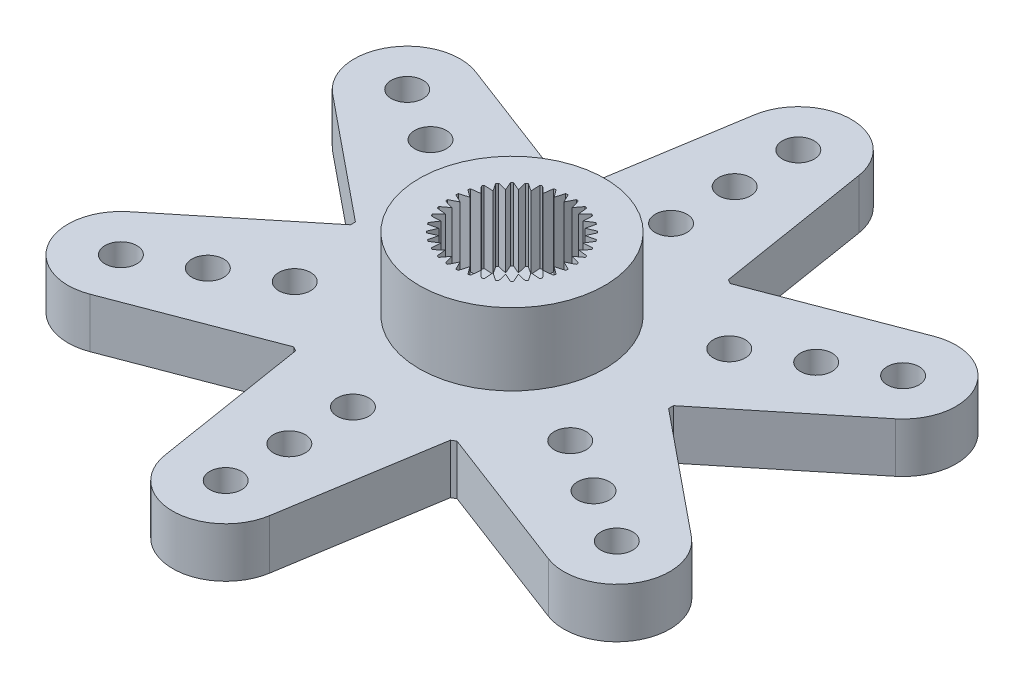
SolidWorks part; units mm, degrees
ref_plane "Front Plane" through (0, 0, 0) normal (0, 0, 1) x (1, 0, 0)
ref_plane "Top Plane" through (0, 0, 0) normal (0, 1, 0) x (1, 0, 0)
ref_plane "Right Plane" through (0, 0, 0) normal (1, 0, 0) x (0, 0, -1)
ref_plane "Plane1" through (0, 2.35, 0) normal (0, 1, 0) x (1, 0, 0)
sketch "Sketch1" plane through (0, 2.35, 0) normal (0, 1, 0) x (1, 0, 0)
  line L0 (-3.65, -6.5519) -> (-2.4683, -13.8971)
  line L1 (2.4683, -13.8971) -> (3.65, -6.5519)
  line L2 (3.8491, -6.4369) -> (10.8011, -9.0861)
  line L3 (13.2694, -4.811) -> (7.4991, -0.115)
  line L4 (7.4991, 0.115) -> (13.2694, 4.811)
  line L5 (10.8011, 9.0861) -> (3.8491, 6.4369)
  line L6 (3.65, 6.5519) -> (2.4683, 13.8971)
  line L7 (-2.4683, 13.8971) -> (-3.65, 6.5519)
  line L8 (-3.8491, 6.4369) -> (-10.8011, 9.0861)
  line L9 (-13.2694, 4.811) -> (-7.4991, 0.115)
  line L10 (-7.4991, -0.115) -> (-13.2694, -4.811)
  line L11 (-10.8011, -9.0861) -> (-3.8491, -6.4369)
  arc A0 (-3.8491, -6.4369) -> (-3.65, -6.5519) centre (0, 0) ccw
  arc A1 (-2.4683, -13.8971) -> (2.4683, -13.8971) centre (0, -13.5) ccw
  arc A2 (3.65, -6.5519) -> (3.8491, -6.4369) centre (0, 0) ccw
  arc A3 (10.8011, -9.0861) -> (13.2694, -4.811) centre (11.6913, -6.75) ccw
  arc A4 (7.4991, -0.115) -> (7.4991, 0.115) centre (0, 0) ccw
  arc A5 (13.2694, 4.811) -> (10.8011, 9.0861) centre (11.6913, 6.75) ccw
  arc A6 (3.8491, 6.4369) -> (3.65, 6.5519) centre (0, 0) ccw
  arc A7 (2.4683, 13.8971) -> (-2.4683, 13.8971) centre (0, 13.5) ccw
  arc A8 (-3.65, 6.5519) -> (-3.8491, 6.4369) centre (0, 0) ccw
  arc A9 (-10.8011, 9.0861) -> (-13.2694, 4.811) centre (-11.6913, 6.75) ccw
  arc A10 (-7.4991, 0.115) -> (-7.4991, -0.115) centre (0, 0) ccw
  arc A11 (-13.2694, -4.811) -> (-10.8011, -9.0861) centre (-11.6913, -6.75) ccw
extrude "Boss-Extrude1" add sketch "Sketch1" against normal blind 2.35
sketch "Sketch2" plane through (0, 2.35, 0) normal (0, 1, 0) x (-1, 0, 0)
  circle A0 centre (0, 0) radius 4.375
extrude "Boss-Extrude2" add sketch "Sketch2" along normal blind 3.4
sketch "Sketch3" plane through (0, 5.75, 0) normal (0, 1, 0) x (-1, 0, 0)
  line L0 (0.6873, 2.7659) -> (0.4254, 2.4128)
  line L1 (0.4254, 2.4128) -> (0.3001, 2.8342)
  line L2 (0.1966, 2.8432) -> (0, 2.45)
  line L3 (0, 2.45) -> (-0.1966, 2.8432)
  line L4 (-0.3001, 2.8342) -> (-0.4254, 2.4128)
  line L5 (-0.4254, 2.4128) -> (-0.6873, 2.7659)
  line L6 (-0.7877, 2.739) -> (-0.8379, 2.3022)
  line L7 (-0.8379, 2.3022) -> (-1.1572, 2.6045)
  line L8 (-1.2513, 2.5606) -> (-1.225, 2.1218)
  line L9 (-1.225, 2.1218) -> (-1.5919, 2.364)
  line L10 (-1.677, 2.3044) -> (-1.5748, 1.8768)
  line L11 (-1.5748, 1.8768) -> (-1.9782, 2.0517)
  line L12 (-2.0517, 1.9782) -> (-1.8768, 1.5748)
  line L13 (-1.8768, 1.5748) -> (-2.3044, 1.677)
  line L14 (-2.364, 1.5919) -> (-2.1218, 1.225)
  line L15 (-2.1218, 1.225) -> (-2.5606, 1.2513)
  line L16 (-2.6045, 1.1572) -> (-2.3022, 0.8379)
  line L17 (-2.3022, 0.8379) -> (-2.739, 0.7877)
  line L18 (-2.7659, 0.6873) -> (-2.4128, 0.4254)
  line L19 (-2.4128, 0.4254) -> (-2.8342, 0.3001)
  line L20 (-2.8432, 0.1966) -> (-2.45, 0)
  line L21 (-2.45, 0) -> (-2.8432, -0.1966)
  line L22 (-2.8342, -0.3001) -> (-2.4128, -0.4254)
  line L23 (-2.4128, -0.4254) -> (-2.7659, -0.6873)
  line L24 (-2.739, -0.7877) -> (-2.3022, -0.8379)
  line L25 (-2.3022, -0.8379) -> (-2.6045, -1.1572)
  line L26 (-2.5606, -1.2513) -> (-2.1218, -1.225)
  line L27 (-2.1218, -1.225) -> (-2.364, -1.5919)
  line L28 (-2.3044, -1.677) -> (-1.8768, -1.5748)
  line L29 (-1.8768, -1.5748) -> (-2.0517, -1.9782)
  line L30 (-1.9782, -2.0517) -> (-1.5748, -1.8768)
  line L31 (-1.5748, -1.8768) -> (-1.677, -2.3044)
  line L32 (-1.5919, -2.364) -> (-1.225, -2.1218)
  line L33 (-1.225, -2.1218) -> (-1.2513, -2.5606)
  line L34 (-1.1572, -2.6045) -> (-0.8379, -2.3022)
  line L35 (-0.8379, -2.3022) -> (-0.7877, -2.739)
  line L36 (-0.6873, -2.7659) -> (-0.4254, -2.4128)
  line L37 (-0.4254, -2.4128) -> (-0.3001, -2.8342)
  line L38 (-0.1966, -2.8432) -> (0, -2.45)
  line L39 (0, -2.45) -> (0.1966, -2.8432)
  line L40 (0.3001, -2.8342) -> (0.4254, -2.4128)
  line L41 (0.4254, -2.4128) -> (0.6873, -2.7659)
  line L42 (0.7877, -2.739) -> (0.8379, -2.3022)
  line L43 (0.8379, -2.3022) -> (1.1572, -2.6045)
  line L44 (1.2513, -2.5606) -> (1.225, -2.1218)
  line L45 (1.225, -2.1218) -> (1.5919, -2.364)
  line L46 (1.677, -2.3044) -> (1.5748, -1.8768)
  line L47 (1.5748, -1.8768) -> (1.9782, -2.0517)
  line L48 (2.0517, -1.9782) -> (1.8768, -1.5748)
  line L49 (1.8768, -1.5748) -> (2.3044, -1.677)
  line L50 (2.364, -1.5919) -> (2.1218, -1.225)
  line L51 (2.1218, -1.225) -> (2.5606, -1.2513)
  line L52 (2.6045, -1.1572) -> (2.3022, -0.8379)
  line L53 (2.3022, -0.8379) -> (2.739, -0.7877)
  line L54 (2.7659, -0.6873) -> (2.4128, -0.4254)
  line L55 (2.4128, -0.4254) -> (2.8342, -0.3001)
  line L56 (2.8432, -0.1966) -> (2.45, 0)
  line L57 (2.45, 0) -> (2.8432, 0.1966)
  line L58 (2.8342, 0.3001) -> (2.4128, 0.4254)
  line L59 (2.4128, 0.4254) -> (2.7659, 0.6873)
  line L60 (2.739, 0.7877) -> (2.3022, 0.8379)
  line L61 (2.3022, 0.8379) -> (2.6045, 1.1572)
  line L62 (2.5606, 1.2513) -> (2.1218, 1.225)
  line L63 (2.1218, 1.225) -> (2.364, 1.5919)
  line L64 (2.3044, 1.677) -> (1.8768, 1.5748)
  line L65 (1.8768, 1.5748) -> (2.0517, 1.9782)
  line L66 (1.9782, 2.0517) -> (1.5748, 1.8768)
  line L67 (1.5748, 1.8768) -> (1.677, 2.3044)
  line L68 (1.5919, 2.364) -> (1.225, 2.1218)
  line L69 (1.225, 2.1218) -> (1.2513, 2.5606)
  line L70 (1.1572, 2.6045) -> (0.8379, 2.3022)
  line L71 (0.8379, 2.3022) -> (0.7877, 2.739)
  arc A0 (0.3001, 2.8342) -> (0.1966, 2.8432) centre (0, 0) ccw
  arc A1 (-0.1966, 2.8432) -> (-0.3001, 2.8342) centre (0, 0) ccw
  arc A2 (-0.6873, 2.7659) -> (-0.7877, 2.739) centre (0, 0) ccw
  arc A3 (-1.1572, 2.6045) -> (-1.2513, 2.5606) centre (0, 0) ccw
  arc A4 (-1.5919, 2.364) -> (-1.677, 2.3044) centre (0, 0) ccw
  arc A5 (-1.9782, 2.0517) -> (-2.0517, 1.9782) centre (0, 0) ccw
  arc A6 (-2.3044, 1.677) -> (-2.364, 1.5919) centre (0, 0) ccw
  arc A7 (-2.5606, 1.2513) -> (-2.6045, 1.1572) centre (0, 0) ccw
  arc A8 (-2.739, 0.7877) -> (-2.7659, 0.6873) centre (0, 0) ccw
  arc A9 (-2.8342, 0.3001) -> (-2.8432, 0.1966) centre (0, 0) ccw
  arc A10 (-2.8432, -0.1966) -> (-2.8342, -0.3001) centre (0, 0) ccw
  arc A11 (-2.7659, -0.6873) -> (-2.739, -0.7877) centre (0, 0) ccw
  arc A12 (-2.6045, -1.1572) -> (-2.5606, -1.2513) centre (0, 0) ccw
  arc A13 (-2.364, -1.5919) -> (-2.3044, -1.677) centre (0, 0) ccw
  arc A14 (-2.0517, -1.9782) -> (-1.9782, -2.0517) centre (0, 0) ccw
  arc A15 (-1.677, -2.3044) -> (-1.5919, -2.364) centre (0, 0) ccw
  arc A16 (-1.2513, -2.5606) -> (-1.1572, -2.6045) centre (0, 0) ccw
  arc A17 (-0.7877, -2.739) -> (-0.6873, -2.7659) centre (0, 0) ccw
  arc A18 (-0.3001, -2.8342) -> (-0.1966, -2.8432) centre (0, 0) ccw
  arc A19 (0.1966, -2.8432) -> (0.3001, -2.8342) centre (0, 0) ccw
  arc A20 (0.6873, -2.7659) -> (0.7877, -2.739) centre (0, 0) ccw
  arc A21 (1.1572, -2.6045) -> (1.2513, -2.5606) centre (0, 0) ccw
  arc A22 (1.5919, -2.364) -> (1.677, -2.3044) centre (0, 0) ccw
  arc A23 (1.9782, -2.0517) -> (2.0517, -1.9782) centre (0, 0) ccw
  arc A24 (2.3044, -1.677) -> (2.364, -1.5919) centre (0, 0) ccw
  arc A25 (2.5606, -1.2513) -> (2.6045, -1.1572) centre (0, 0) ccw
  arc A26 (2.739, -0.7877) -> (2.7659, -0.6873) centre (0, 0) ccw
  arc A27 (2.8342, -0.3001) -> (2.8432, -0.1966) centre (0, 0) ccw
  arc A28 (2.8432, 0.1966) -> (2.8342, 0.3001) centre (0, 0) ccw
  arc A29 (2.7659, 0.6873) -> (2.739, 0.7877) centre (0, 0) ccw
  arc A30 (2.6045, 1.1572) -> (2.5606, 1.2513) centre (0, 0) ccw
  arc A31 (2.364, 1.5919) -> (2.3044, 1.677) centre (0, 0) ccw
  arc A32 (2.0517, 1.9782) -> (1.9782, 2.0517) centre (0, 0) ccw
  arc A33 (1.677, 2.3044) -> (1.5919, 2.364) centre (0, 0) ccw
  arc A34 (1.2513, 2.5606) -> (1.1572, 2.6045) centre (0, 0) ccw
  arc A35 (0.7877, 2.739) -> (0.6873, 2.7659) centre (0, 0) ccw
extrude "Cut-Extrude1" cut sketch "Sketch3" against normal blind 3.4
hole_wizard "Hole1" positions "Sketch5" profile "Sketch4" legacy
sketch "Sketch5" plane through (0, 0, 0) normal (0, -1, 0) x (-1, 0, 0)
  point P0 (0, 0)
sketch "Sketch4" plane through (0, 0, 0) normal (1, 0, 0) x (0, 0, -1)
  line L0 (0, 0) -> (0, 0.3)
  line L1 (0, 0.3) -> (4.4, 0.3)
  line L2 (4.4, 0.3) -> (4.4, 0)
  line L3 (4.4, 0) -> (0, 0)
  line L4 (0, 110) -> (0, -10) construction
  dimension "Diameter" = 8.8
  dimension "Depth" = 0.3
sketch "Sketch6" plane through (0, 0, 0) normal (0, 0, 1) x (1, 0, 0)
  line L0 (3.25, 0.3) -> (0, 0.3)
  line L1 (0, 0.3) -> (0, 0)
  line L2 (0, 0) -> (3.25, 0)
  line L3 (3.25, 0) -> (3.25, 0.3)
  line L4 (0, 0.3) -> (0, 0) construction
revolve "Revolve1" add sketch "Sketch6" angle 360 about L4
hole_wizard "#00 Clearance Hole1" positions "Sketch8" profile "Sketch7" hole size "#00" standard "ANSI Inch"
sketch "Sketch8" plane through (0, 2.35, 0) normal (0, 1, 0) x (1, 0, 0)
  point P0 (0, -13.5)
  point P1 (0, -7.5)
  point P2 (0, -10.5)
  point P3 (11.6913, -6.75)
  point P4 (6.4952, -3.75)
  point P5 (9.0933, -5.25)
  point P6 (11.6913, 6.75)
  point P7 (6.4952, 3.75)
  point P8 (9.0933, 5.25)
  point P9 (0, 13.5)
  point P10 (0, 7.5)
  point P11 (0, 10.5)
  point P12 (-11.6913, 6.75)
  point P13 (-6.4952, 3.75)
  point P14 (-9.0933, 5.25)
  point P15 (-11.6913, -6.75)
  point P16 (-6.4952, -3.75)
  point P17 (-9.0933, -5.25)
sketch "Sketch7" plane through (0, 2.35, 13.5) normal (1, 0, 0) x (0, 0, 1)
  line L0 (0, 0) -> (0, 2.35)
  line L1 (0, 2.35) -> (0.75, 2.35)
  line L2 (0.75, 2.35) -> (0.75, 0)
  line L5 (0.75, 0) -> (0, 0)
  line L11 (0, -6.35) -> (0, 107.95) construction
  dimension "Thru Hole Dia." = 1.5
  dimension "Thru Hole Depth" = 2.35
hole_wizard "CBORE for #3 Binding Head Machine Screw1" positions "Sketch10" profile "Sketch9" counterbore size "#3" standard "ANSI Inch"
sketch "Sketch10" plane through (0, 0, 0) normal (0, -1, 0) x (-1, 0, 0)
  point P0 (0, 0)
sketch "Sketch9" plane through (0, 0, 0) normal (1, 0, 0) x (0, 0, -1)
  line L0 (0, 0) -> (0, 5.75)
  line L1 (0, 5.75) -> (1.5, 5.75)
  line L3 (1.5, 5.75) -> (1.5, 0.3)
  line L4 (1.5, 0.3) -> (2.75, 0.3)
  line L5 (2.75, 0.3) -> (2.75, 0)
  line L7 (2.75, 0) -> (0, 0)
  line L11 (0, -6.35) -> (0, 107.95) construction
  dimension "Thru Hole Dia." = 3
  dimension "Thru Hole Depth" = 5.75
  dimension "C'Bore Dia." = 5.5
  dimension "C'Bore Depth" = 0.3
